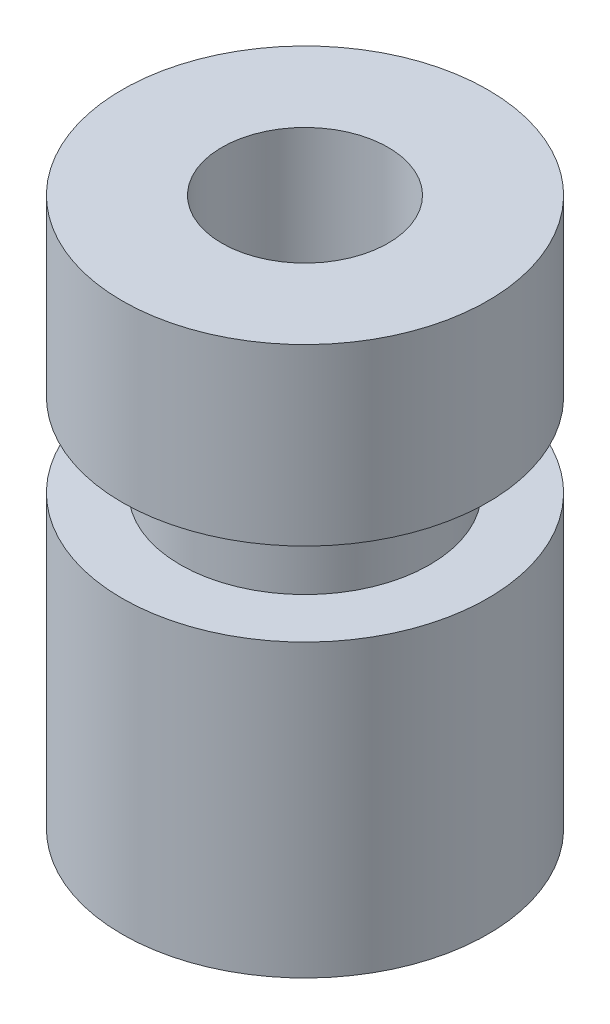
SolidWorks part; units mm, degrees
ref_plane "前视基准面" through (0, 0, 0) normal (0, 0, 1) x (1, 0, 0)
ref_plane "上视基准面" through (0, 0, 0) normal (0, 1, 0) x (1, 0, 0)
ref_plane "右视基准面" through (0, 0, 0) normal (1, 0, 0) x (0, 0, -1)
other "Configuration Table"
sketch "草图2" plane through (0, 0, 0) normal (0, 0, 1) x (1, 0, 0)
  line L0 (0, 1.7453) -> (0, -1.4811) construction
  line L1 (0, 6.6) -> (1, 6.6) construction
  line L2 (1, 6.6) -> (1, 0)
  line L3 (1, 0) -> (0, 0) construction
  line L5 (1, 6.6) -> (2.2, 6.6)
  line L6 (2.2, 6.6) -> (2.2, 4.5)
  line L7 (2.2, 4.5) -> (1.5, 4.5)
  line L8 (1.5, 4.5) -> (1.5, 3.5)
  line L9 (1.5, 3.5) -> (2.2, 3.5)
  line L10 (2.2, 3.5) -> (2.2, 0)
  line L11 (2.2, 0) -> (1, 0)
  dimension "D1" = 1
  dimension "D2" = 1.5
  dimension "D3" = 2.2
  dimension "D4" = 3.5
  dimension "D5" = 1
  dimension "D6" = 6.6
revolve "旋转1" add sketch "草图2" angle 360 about L0
